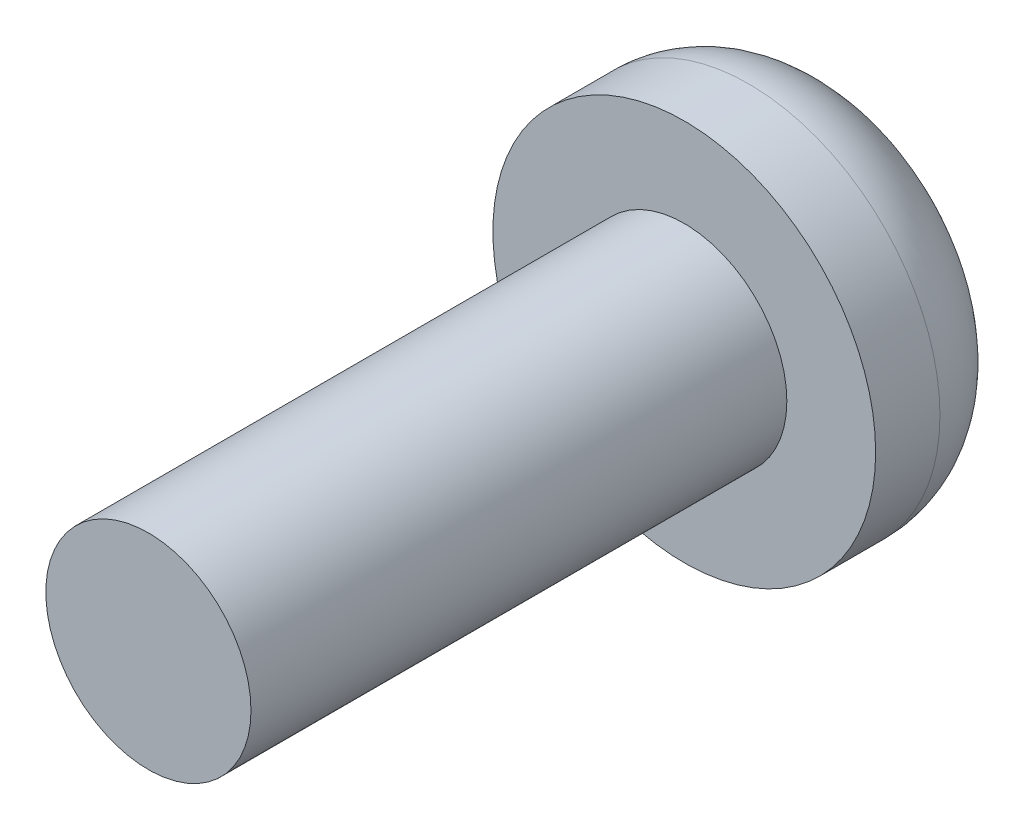
SolidWorks part; units mm, degrees
ref_plane "Front Plane" through (0, 0, 0) normal (0, 0, 1) x (1, 0, 0)
ref_plane "Top Plane" through (0, 0, 0) normal (0, 1, 0) x (1, 0, 0)
ref_plane "Right Plane" through (0, 0, 0) normal (1, 0, 0) x (0, 0, -1)
sketch "Sketch1" plane through (0, 0, 0) normal (0, 0, 1) x (1, 0, 0)
  circle A0 centre (0, 0) radius 3.175
  dimension "D1" = 6.35
extrude "Extrude1" add sketch "Sketch1" along normal blind 2.5908
fillet "Fillet1" radius 1.524 1 edges at (3.175, 0, 0)
sketch "Sketch2" plane through (0, 0, 2.5908) normal (0, 0, 1) x (1, 0, 0)
  circle A0 centre (0, 0) radius 1.7018
  dimension "D1" = 3.4036
extrude "Extrude2" add sketch "Sketch2" along normal blind 8.89
sketch "Sketch3" plane through (0, 0, 0) normal (0, 0, -1) x (-1, 0, 0)
  line L1 (1.6382, 0.2053) -> (-1.6382, 0.2053)
  line L2 (1.6382, 0.2053) -> (1.6382, -0.2053)
  line L3 (1.6382, -0.2053) -> (-1.6382, -0.2053)
  line L4 (-1.6382, 0.2053) -> (-1.6382, -0.2053)
  line L5 (1.6382, 0.2053) -> (-1.6382, -0.2053) construction
  line L6 (1.6382, -0.2053) -> (-1.6382, 0.2053) construction
  circle A0 centre (0, 0) radius 1.651 construction
  point P0 (0, 0)
  point P8 (0, 0)
extrude "Extrude3" cut sketch "Sketch3" against normal blind 1.016
pattern_circular "CirPattern1" count 2 over 90 about axis through (0, 0, 0) along (0, 0, 1) of "Extrude3"
